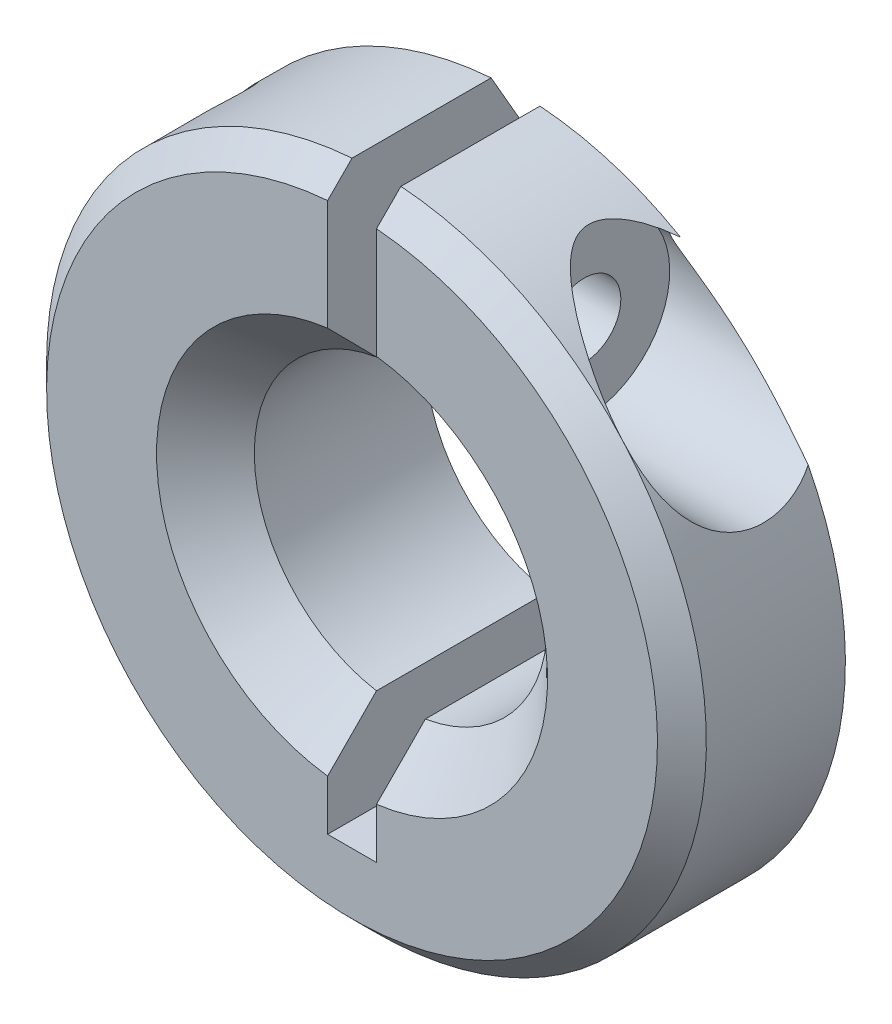
SolidWorks part; units mm, degrees
ref_plane "Face" through (0, 0, 0) normal (0, 0, 1) x (1, 0, 0)
ref_plane "Dessus" through (0, 0, 0) normal (0, 1, 0) x (1, 0, 0)
ref_plane "Droite" through (0, 0, 0) normal (1, 0, 0) x (0, 0, -1)
sketch "Esquisse1" plane through (0, 0, 0) normal (0, 0, 1) x (1, 0, 0)
  circle A0 centre (0, 0) radius 6.75
  circle A1 centre (0, 0) radius 3
  dimension "D1" = 13.5
  dimension "D2" = 6
extrude "Extrusion1" add sketch "Esquisse1" along normal blind 4.5
chamfer "Chanfrein1" distance 2 angle 30 1 edges at (6.75, 0, 0)
sketch "Esquisse3" plane through (0, 0, 4.5) normal (0, 0, 1) x (1, 0, 0)
  line L0 (0, 6.75) -> (0, -6.75) construction
  line L1 (-0.5, 6.7315) -> (-0.5, -5)
  line L2 (0.5, 6.7315) -> (0.5, -5)
  line L3 (0.5, -5) -> (-0.5, -5)
  circle A0 centre (0, 0) radius 6.75 construction
  arc A1 (-0.5, 6.7315) -> (0.5, 6.7315) centre (0, 0) cw
  dimension "D1" = 0.5
  dimension "D2" = 5
extrude "Enlèv. mat.-Extru.1" cut sketch "Esquisse3" against normal up to next
chamfer "Chanfrein3" distance 0.5 angle 45 1 edges at (0, -6.75, 4.5)
hole_wizard "Trou taraudé M1.61" positions "Esquisse6" profile "Esquisse7" tap size "M1.6" standard "ISO"
sketch "Esquisse6" plane through (-0.5, 0, 0) normal (1, 0, 0) x (0, 0, -1)
  line L0 (-4.5, 6.23) -> (-4.5, 2.958) construction
  line L1 (-1.1547, 6.7315) -> (-4, 6.7315) construction
  point P0 (-2.25, 4.4815)
  dimension "D1" = 2.25
  dimension "D2" = 2.25
sketch "Esquisse7" plane through (-0.5, 4.4815, 2.25) normal (0, 1, 0) x (0, 0, -1)
  line L0 (0, 0) -> (0, 6.25)
  line L1 (0, 6.25) -> (0.625, 6.25)
  line L2 (0.625, 6.25) -> (0.625, 0)
  line L5 (0.625, 0) -> (0, 0)
  line L11 (0, -6.35) -> (0, 107.95) construction
  dimension "Diamètre du trou pour taraudage jusqu'au prochain" = 1.25
  dimension "Profondeur du trou pour taraudage jusqu'au prochain" = 6.25
cosmetic thread "Filetage de perçage1" parameters "D2"=1.6
sketch "Esquisse8" plane through (0.5, 0, 0) normal (-1, 0, 0) x (0, 0, 1)
  circle A0 centre (2.25, 4.4815) radius 1.75
  circle A1 centre (2.25, 4.4815) radius 0.625 construction
  dimension "D1" = 3.5
extrude "Enlèv. mat.-Extru.3" cut sketch "Esquisse8" against normal up to next
sketch "Esquisse9" plane through (0.5, 0, 0) normal (-1, 0, 0) x (0, 0, 1)
  circle A0 centre (2.25, 4.4815) radius 1.75
  circle A1 centre (2.25, 4.4815) radius 0.75
  circle A2 centre (2.25, 4.4815) radius 1.75 construction
  dimension "D1" = 1.5
extrude "Extrusion2" add sketch "Esquisse9" against normal blind 2
chamfer "Chanfrein4" distance 1 angle 45 2 edges at (3, 0, 4.5) (-3, 0, 4.5)
sketch "Esquisse10" plane through (0, 0, 4.5) normal (0, 0, 1) x (1, 0, 0)
  circle A0 centre (0, 0) radius 3
  arc A1 (-0.5, 2.958) -> (-0.5, -2.958) centre (0, 0) ccw construction
extrude "Enlèv. mat.-Extru.4" cut sketch "Esquisse10" against normal through all
